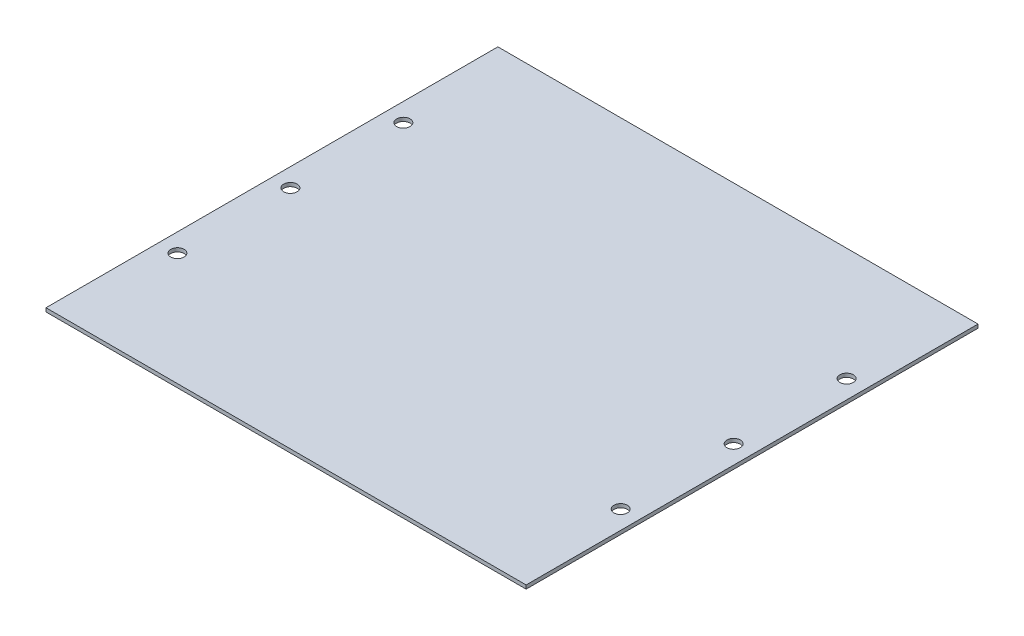
SolidWorks part; units mm, degrees
ref_plane "Front Plane" through (0, 0, 0) normal (0, 0, 1) x (1, 0, 0)
ref_plane "Top Plane" through (0, 0, 0) normal (0, 1, 0) x (1, 0, 0)
ref_plane "Right Plane" through (0, 0, 0) normal (1, 0, 0) x (0, 0, -1)
sketch "Sketch4" plane through (0, 0, 0) normal (0, 1, 0) x (1, 0, 0)
  line L1 (-305.3335, -151.6881) -> (18.5165, -151.6881)
  line L2 (-305.3335, -151.6881) -> (-305.3335, -456.4881)
  line L3 (-305.3335, -456.4881) -> (18.5165, -456.4881)
  line L4 (18.5165, -151.6881) -> (18.5165, -456.4881)
  circle A0 centre (-292.8875, -227.8881) radius 4.5198
  circle A1 centre (-292.8875, -304.0881) radius 4.5198
  circle A2 centre (-292.8875, -380.2881) radius 4.5198
  circle A3 centre (6.0705, -227.8881) radius 4.5198
  circle A4 centre (6.0705, -304.0881) radius 4.5198
  circle A5 centre (6.0705, -380.2881) radius 4.5198
  dimension "D3" = 76.2
  dimension "D4" = 76.2
  dimension "D5" = 76.2
  dimension "D6" = 12.446
  dimension "D7" = 12.446
  dimension "D8" = 12.446
  dimension "D9" = 12.446
  dimension "D10" = 12.446
  dimension "D11" = 12.446
  dimension "D12" = 76.2
  dimension "D13" = 76.2
  dimension "D1" = 323.85
  dimension "D2" = 304.8
  dimension "D14" = 76.2
extrude "Boss-Extrude3" add sketch "Sketch4" along normal blind 2.4765
